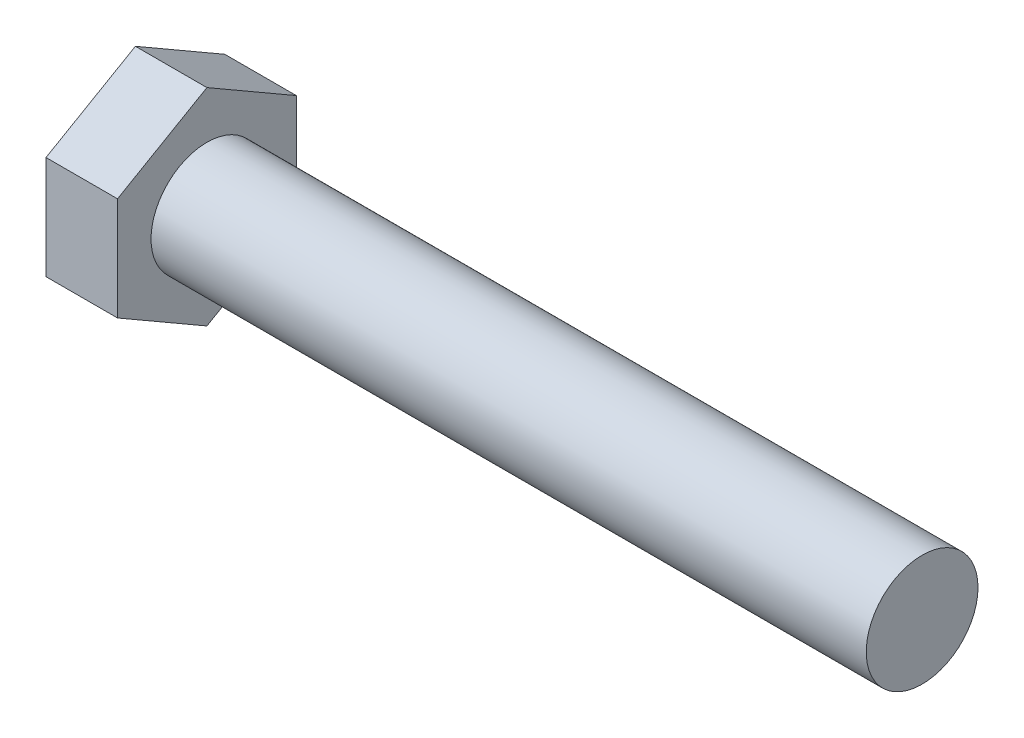
SolidWorks part; units mm, degrees
ref_plane "Front Plane" through (0, 0, 0) normal (0, 0, 1) x (1, 0, 0)
ref_plane "Top Plane" through (0, 0, 0) normal (0, 1, 0) x (1, 0, 0)
ref_plane "Right Plane" through (0, 0, 0) normal (1, 0, 0) x (0, 0, -1)
sketch "Sketch1" plane through (0, 0, 0) normal (1, 0, 0) x (0, 0, -1)
  line L1 (6.35, 3.6662) -> (0, 7.3323)
  line L2 (0, 7.3323) -> (-6.35, 3.6662)
  line L3 (-6.35, 3.6662) -> (-6.35, -3.6662)
  line L4 (-6.35, -3.6662) -> (0, -7.3323)
  line L5 (0, -7.3323) -> (6.35, -3.6662)
  line L6 (6.35, -3.6662) -> (6.35, 3.6662)
  circle A0 centre (0, 0) radius 6.35 construction
  point P1 (3.175, -5.4993)
  dimension "D1" = 6.35
  dimension "D2" = 7.3323
extrude "Boss-Extrude1" add sketch "Sketch1" along normal blind 5.08
sketch "Sketch2" plane through (5.08, 0, 0) normal (1, 0, 0) x (0, 0, -1)
  circle A0 centre (0, 0) radius 3.9688
  dimension "D1" = 7.9375
extrude "Boss-Extrude2" add sketch "Sketch2" along normal blind 50.8
